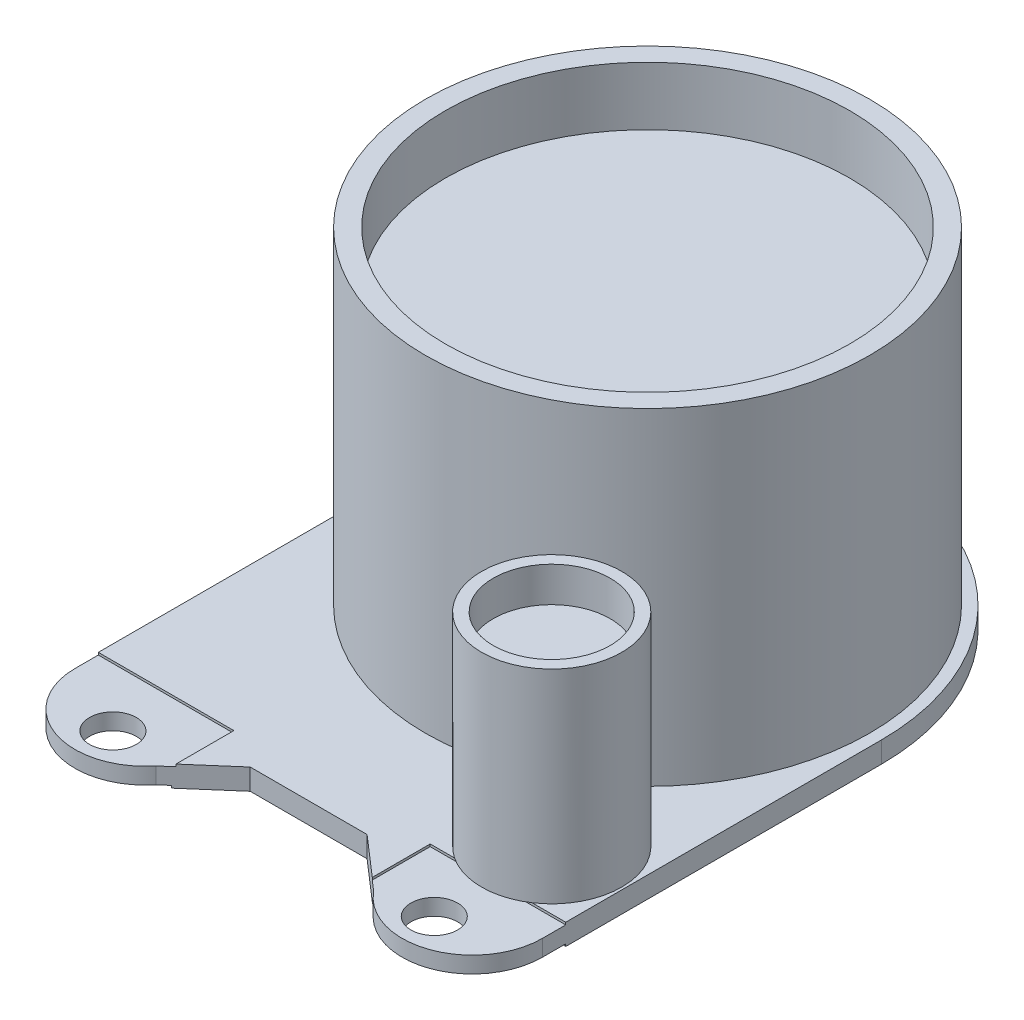
SolidWorks part; units mm, degrees
ref_plane "Plan de face" through (0, 0, 0) normal (0, 0, 1) x (1, 0, 0)
ref_plane "Plan de dessus" through (0, 0, 0) normal (0, 1, 0) x (1, 0, 0)
ref_plane "Plan de droite" through (0, 0, 0) normal (1, 0, 0) x (0, 0, -1)
sketch "Esquisse1" plane through (0, 0, 0) normal (0, 1, 0) x (1, 0, 0)
  line L0 (-10, 0) -> (-10, -14.5)
  line L1 (10, 0) -> (10, -14.5)
  line L2 (-4.6609, -16.3784) -> (-2.5, -14.5)
  line L3 (-2.5, -14.5) -> (2.5, -14.5)
  line L4 (2.5, -14.5) -> (4.6609, -16.3784)
  arc A0 (-10, 0) -> (10, 0) centre (0, 0) cw
  arc A1 (-10, -14.5) -> (-4.6609, -16.3784) centre (-7, -14.5) ccw
  arc A2 (10, -14.5) -> (4.6609, -16.3784) centre (7, -14.5) cw
  circle A3 centre (-6.875, -16) radius 1
  circle A4 centre (6.875, -16) radius 1
  point P15 (6.875, -14.4051)
  point P17 (-6.875, -17.1169)
  point P18 (7, -16.4311)
  point P19 (-4.915, -17.1571)
  point P20 (0, -14.5)
  point P21 (-4.6745, -16.8952)
  dimension "D6" = 3
  dimension "D7" = 3
  dimension "D9" = 2
  dimension "D1" = 20
  dimension "D2" = 10
  dimension "D3" = 14.5
  dimension "D4" = 13.75
  dimension "D5" = 6.875
  dimension "D8" = 5
  dimension "D10" = 139
  dimension "D11" = 16
extrude "Boss.-Extru.1" add sketch "Esquisse1" along normal blind 0.9
sketch "Esquisse2" plane through (0, 0.9, 0) normal (0, 1, 0) x (1, 0, 0)
  circle A0 centre (0, 0) radius 9.5
  dimension "D1" = 19
extrude "Boss.-Extru.2" add sketch "Esquisse2" along normal blind 14
sketch "Esquisse3" plane through (0, 14.9, 0) normal (0, 1, 0) x (1, 0, 0)
  circle A0 centre (0, 0) radius 8.65
  dimension "D1" = 17.3
extrude "Enlèv. mat.-Extru.1" cut sketch "Esquisse3" against normal blind 2.5
sketch "Esquisse5" plane through (0, 0.9, 0) normal (0, 1, 0) x (1, 0, 0)
  line L0 (10, -14.5) -> (10, 0) construction
  circle A0 centre (6.9, -11) radius 3
  circle A1 centre (6.875, -16) radius 1 construction
  point P4 (0, 0)
  dimension "D1" = 6
  dimension "D3" = 5
  dimension "D2" = 3.1
extrude "Boss.-Extru.3" add sketch "Esquisse5" along normal blind 8.7
sketch "Esquisse6" plane through (0, 9.6, 0) normal (0, 1, 0) x (1, 0, 0)
  circle A0 centre (6.9, -11) radius 2.5
  circle A1 centre (6.9, -11) radius 3 construction
  dimension "D1" = 5
extrude "Enlèv. mat.-Extru.2" cut sketch "Esquisse6" against normal blind 1.5
sketch "Esquisse7" plane through (0, 0, 0) normal (0, -1, 0) x (1, 0, 0)
  line L0 (10, 14.5) -> (10, 0) construction
  line L1 (-10, 18.5) -> (-4.3, 18.5)
  line L2 (-10, 18.5) -> (-10, 13.5)
  line L3 (-10, 13.5) -> (-4.3, 13.5)
  line L4 (-4.3, 18.5) -> (-4.3, 13.5)
  line L5 (4.3, 18.5) -> (10, 18.5)
  line L6 (4.3, 18.5) -> (4.3, 13.5)
  line L7 (4.3, 13.5) -> (10, 13.5)
  line L8 (10, 18.5) -> (10, 13.5)
  line L9 (-10, 0) -> (-10, 14.5) construction
  line L10 (-2.5, 14.5) -> (2.5, 14.5) construction
  circle A0 centre (0, 0) radius 4.25
  dimension "D1" = 8.5
  dimension "D2" = 5.7
  dimension "D3" = 5.7
  dimension "D4" = 1
  dimension "D5" = 5
extrude "Enlèv. mat.-Extru.3" cut sketch "Esquisse7" against normal blind 0.1
sketch "Esquisse8" plane through (0, 0.9, 0) normal (0, 1, 0) x (1, 0, 0)
  line L0 (-10, 0) -> (-10, -14.5) construction
  line L1 (-10, -13.5) -> (-4.2, -13.5)
  line L2 (-10, -13.5) -> (-10, -18.5)
  line L3 (-10, -18.5) -> (-4.2, -18.5)
  line L4 (-4.2, -13.5) -> (-4.2, -18.5)
  line L5 (10, -14.5) -> (10, 0) construction
  line L6 (10, -13.5) -> (4.2, -13.5)
  line L7 (10, -13.5) -> (10, -18.5)
  line L8 (10, -18.5) -> (4.2, -18.5)
  line L9 (4.2, -13.5) -> (4.2, -18.5)
  line L10 (-2.5, -14.5) -> (2.5, -14.5) construction
  dimension "D1" = 1
  dimension "D2" = 5.8
  dimension "D3" = 5.8
  dimension "D4" = 5
extrude "Enlèv. mat.-Extru.4" cut sketch "Esquisse8" against normal blind 0.1
